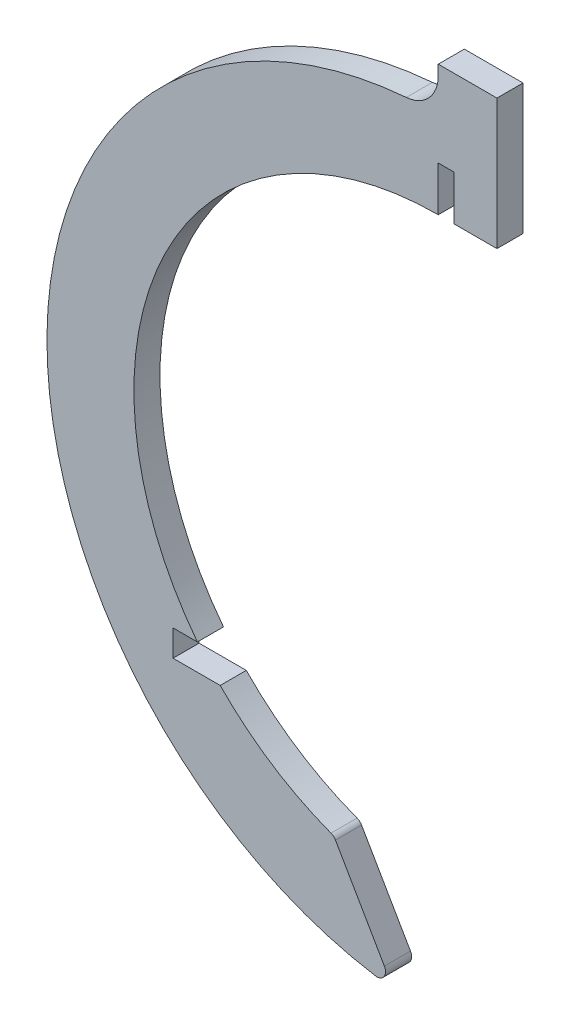
SolidWorks part; units mm, degrees
ref_plane "Front Plane" through (0, 0, 0) normal (0, 0, 1) x (1, 0, 0)
ref_plane "Top Plane" through (0, 0, 0) normal (0, 1, 0) x (1, 0, 0)
ref_plane "Right Plane" through (0, 0, 0) normal (1, 0, 0) x (0, 0, -1)
sketch "Sketch1" plane through (0, 0, 0) normal (0, 0, 1) x (1, 0, 0)
  line L0 (0, 40.1549) -> (0, 35)
  line L1 (0, 40.1549) -> (1.79, 40.1549)
  line L2 (1.79, 40.1549) -> (1.79, 35)
  line L3 (1.79, 35) -> (6.75, 35)
  line L4 (6.75, 35) -> (6.75, 50)
  line L5 (6.75, 50) -> (0, 50)
  line L6 (0, 50) -> (0, 45)
  line L7 (-15.5227, -26.7768) -> (-3.9352, -46.847)
  line L8 (-5.0015, -45) -> (-75.6675, -45) construction
  line L9 (0, -35) -> (0, -45)
  arc A0 (0, 35) -> (0, -35) centre (0, 0) ccw
  arc A1 (0, 45) -> (0, -45) centre (0, 0) ccw
  dimension "D1" = 70
  dimension "D2" = 10
  dimension "D3" = 5
  dimension "D4" = 15
  dimension "D5" = 6.75
  dimension "D6" = 4.96
  dimension "D7" = 1.79
  dimension "D8" = 60
extrude "Boss-Extrude1" add sketch "Sketch1" along normal blind 3 contours L6 A1 L7 A0 L0 L1 L2 L3 L4 L5
fillet "Fillet1" radius 4 1 edges at (0, 45, 1.5)
fillet "Fillet2" radius 1 1 edges at (-5.1738, -44.7016, 1.5)
fillet "Fillet3" radius 1 1 edges at (-11.9998, -32.8786, 1.5)
sketch "Sketch2" plane through (0, 0, 3) normal (0, 0, 1) x (1, 0, 0)
  line L0 (-7.2236, -44.4164) -> (-85.9393, -44.4164) construction
  line L1 (-34, -21.3964) -> (34.7661, -21.3964)
  line L2 (-34, -21.3964) -> (-34, -24.4164)
  line L3 (-34, -24.4164) -> (34.7661, -24.4164)
  line L4 (34.7661, -21.3964) -> (34.7661, -24.4164)
  arc A0 (-3.6735, 44.8498) -> (-7.2236, -44.4164) centre (0, 0) ccw construction
  dimension "D1" = 20
  dimension "D2" = 3.02
  dimension "30" = 34
extrude "Cut-Extrude3" cut sketch "Sketch2" against normal blind 10
sketch "Sketch3" plane through (0, 0, 3) normal (0, 0, 1) x (1, 0, 0)
  line L0 (-34, -24.4164) -> (-25.0766, -24.4164) construction
  line L1 (-34, -21.3964) -> (-30.5, -21.3964)
  line L2 (-34, -21.3964) -> (-34, -24.4164)
  line L3 (-34, -24.4164) -> (-30.5, -24.4164)
  line L4 (-30.5, -21.3964) -> (-30.5, -24.4164)
  dimension "D1" = 3.5
extrude "Boss-Extrude2" add sketch "Sketch3" against normal blind 3
